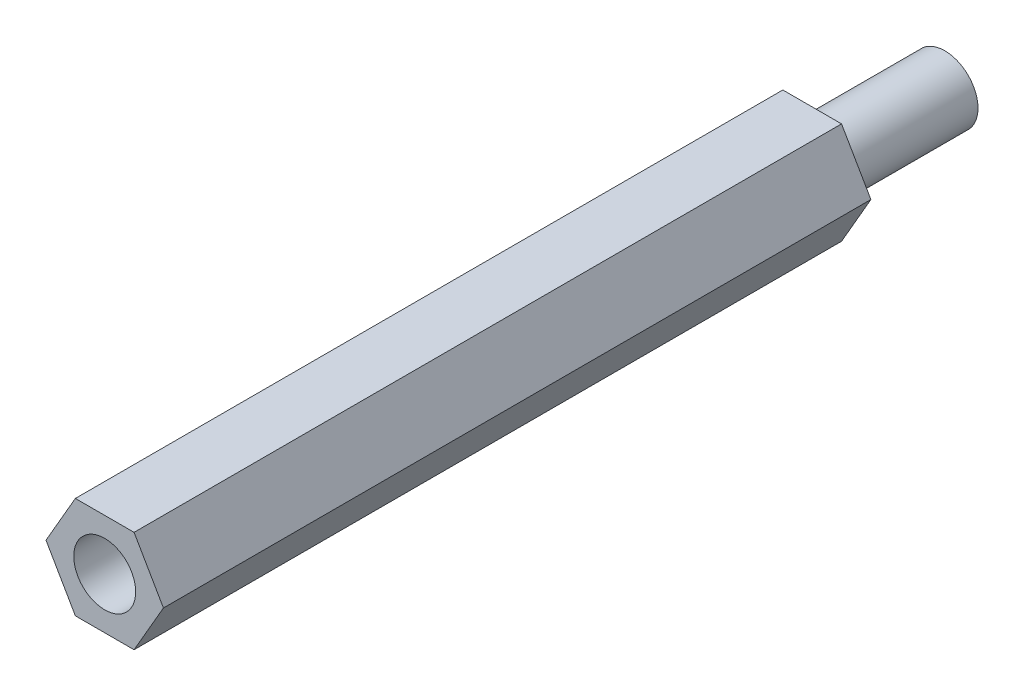
SolidWorks part; units mm, degrees
ref_plane "前视基准面" through (0, 0, 0) normal (0, 0, 1) x (1, 0, 0)
ref_plane "上视基准面" through (0, 0, 0) normal (0, 1, 0) x (1, 0, 0)
ref_plane "右视基准面" through (0, 0, 0) normal (1, 0, 0) x (0, 0, -1)
sketch "草图1" plane through (0, 0, 0) normal (0, 0, 1) x (1, 0, 0)
  line L1 (2.6558, 0) -> (1.3279, 2.3)
  line L2 (1.3279, 2.3) -> (-1.3279, 2.3)
  line L3 (-1.3279, 2.3) -> (-2.6558, 0)
  line L4 (-2.6558, 0) -> (-1.3279, -2.3)
  line L5 (-1.3279, -2.3) -> (1.3279, -2.3)
  line L6 (1.3279, -2.3) -> (2.6558, 0)
  circle A0 centre (0, 0) radius 2.3 construction
  circle A1 centre (0, 0) radius 1.4
  dimension "D1" = 2.8
  dimension "D2" = 4.6
extrude "凸台-拉伸1" add sketch "草图1" along normal blind 32
sketch "草图2" plane through (0, 0, 0) normal (0, 0, -1) x (-1, 0, 0)
  circle A0 centre (0, 0) radius 1.5
  dimension "D1" = 3
extrude "凸台-拉伸2" add sketch "草图2" along normal blind 6
